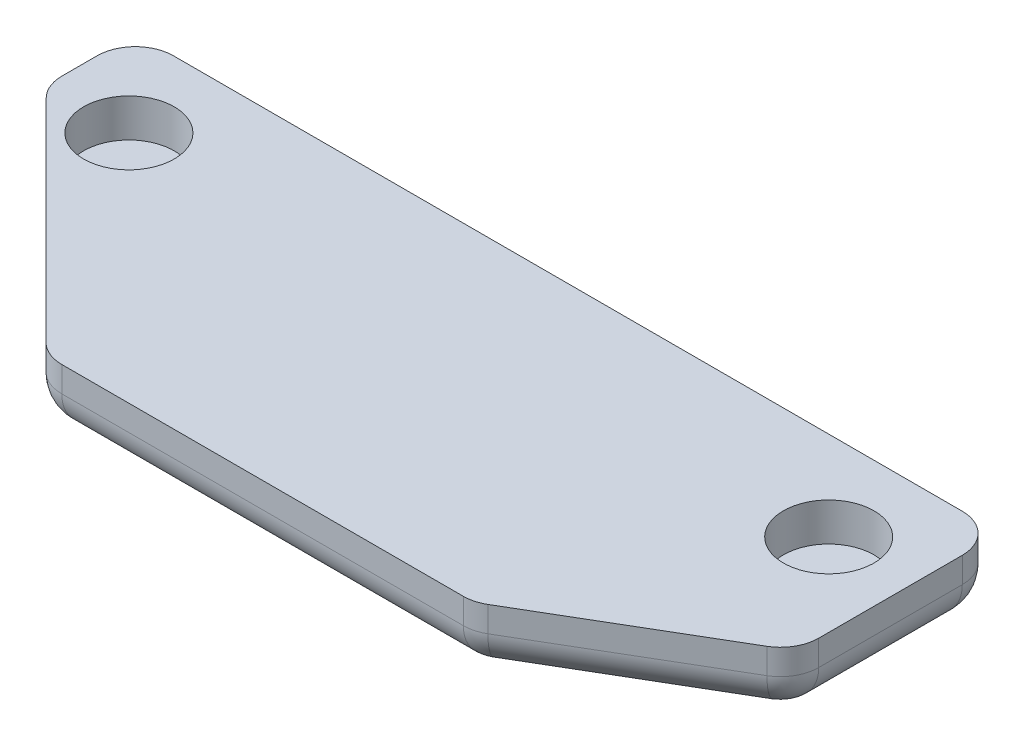
SolidWorks part; units mm, degrees
ref_plane "Front Plane" through (0, 0, 0) normal (0, 0, 1) x (1, 0, 0)
ref_plane "Top Plane" through (0, 0, 0) normal (0, 1, 0) x (1, 0, 0)
ref_plane "Right Plane" through (0, 0, 0) normal (1, 0, 0) x (0, 0, -1)
sketch "Sketch2" plane through (0, 0, 0) normal (0, 1, 0) x (1, 0, 0)
  line L0 (-21.2162, 11.7419) -> (-21.2162, 8.2419)
  line L1 (-21.2162, 8.2419) -> (-12.0249, -0.9581)
  line L2 (-12.0249, -0.9581) -> (4.7838, -0.9581)
  line L3 (4.7838, -0.9581) -> (12.7838, 3.7419)
  line L4 (12.7838, 3.7419) -> (12.7838, 11.7419)
  line L7 (-21.2162, 11.7419) -> (12.7838, 11.7419)
  dimension "D1" = 34
  dimension "D2" = 12.7
  dimension "D3" = 8
  dimension "D4" = 8
  dimension "D5" = 3.5
  dimension "D6" = 9.1913
extrude "Boss-Extrude1" add sketch "Sketch2" along normal blind 2.5
sketch "Sketch4" plane through (0, 2.5, 0) normal (0, 1, 0) x (1, 0, 0)
  line L0 (-17.9662, 11.241) -> (-17.9662, -1.2869) construction
  line L1 (-21.2162, 8.2419) -> (12.7838, 8.2419) construction
  line L2 (-21.2162, 11.7419) -> (-21.2162, 8.2419) construction
  line L3 (12.7838, 11.7419) -> (-21.2162, 11.7419) construction
  line L4 (-4.2162, 11.7419) -> (-4.2162, -0.9581) construction
  line L5 (-12.0249, -0.9581) -> (4.7838, -0.9581) construction
  line L6 (9.5338, 11.241) -> (9.5338, -1.2869) construction
  circle A0 centre (-17.9662, 8.2419) radius 1.78
  circle A1 centre (9.5338, 8.2419) radius 1.78
  point P15 (-4.2162, 8.2419)
  dimension "D1" = 3.25
  dimension "D2" = 3.5
extrude "Cut-Extrude1" cut sketch "Sketch4" against normal blind 1.5
fillet "Fillet1" radius 1.5 12 edges at (4.7838, 1.25, 0.9581) (-12.0249, 1.25, 0.9581) (-21.2162, 0, -9.9919) (-16.6205, 0, -3.6419) (-3.6205, 0, 0.9581) (8.7838, 0, -1.3919) (12.7838, 1.25, -3.7419) (12.7838, 0, -7.7419) (-4.2162, 0, -11.7419) (12.7838, 1.25, -11.7419) (-21.2162, 1.25, -8.2419) (-21.2162, 1.25, -11.7419)
